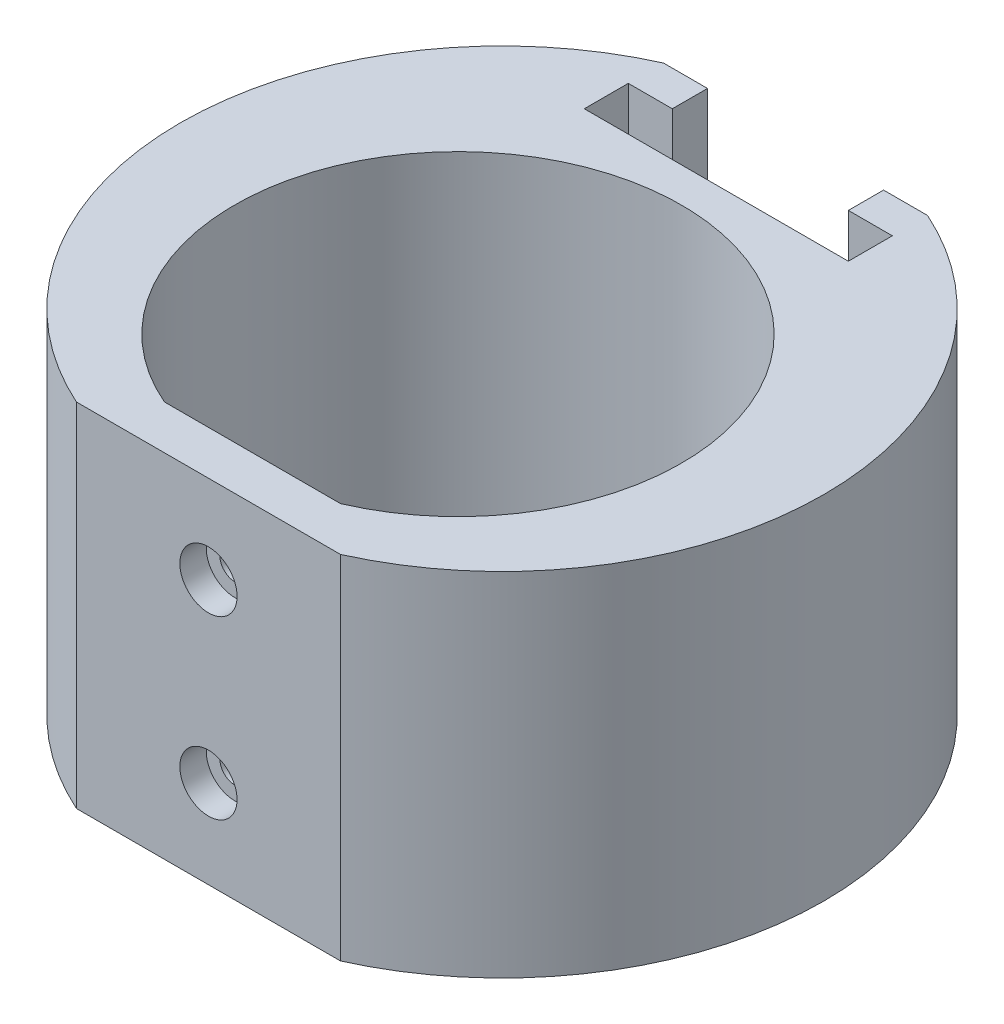
SolidWorks part; units mm, degrees
ref_plane "Front Plane" through (0, 0, 0) normal (0, 0, 1) x (1, 0, 0)
ref_plane "Top Plane" through (0, 0, 0) normal (0, 1, 0) x (1, 0, 0)
ref_plane "Right Plane" through (0, 0, 0) normal (1, 0, 0) x (0, 0, -1)
sketch "Sketch1" plane through (0, 0, 0) normal (0, 1, 0) x (1, 0, 0)
  line L0 (-10, -23.3487) -> (10, -23.3487)
  line L1 (-15, -28.3487) -> (15, -28.3487)
  line L2 (-15, 38.3487) -> (15, 38.3487)
  arc A0 (10, -23.3487) -> (-10, -23.3487) centre (0, 0) ccw
  arc A1 (15, -28.3487) -> (15, 38.3487) centre (0, 5) ccw
  arc A2 (-15, 38.3487) -> (-15, -28.3487) centre (0, 5) ccw
  dimension "D1" = 25.4
  dimension "D4" = 30
  dimension "D2" = 20
  dimension "D3" = 5
  dimension "D5" = 5
  dimension "D6" = 30
extrude "Boss-Extrude1" add sketch "Sketch1" along normal mid plane 40
ref_plane "Plane1" through (0, 0, -41.5668) normal (0, 0, -1) x (-1, 0, 0)
sketch "Sketch2" plane through (0, 0, -41.5668) normal (0, 0, -1) x (-1, 0, 0)
  line L1 (-10, -7.5) -> (10, -7.5)
  line L2 (-10, -7.5) -> (-10, 7.5)
  line L3 (-10, 7.5) -> (10, 7.5)
  line L4 (10, -7.5) -> (10, 7.5)
  line L5 (-10, -7.5) -> (10, 7.5) construction
  line L6 (-10, 7.5) -> (10, -7.5) construction
  point P0 (0, 0)
  dimension "D1" = 20
  dimension "D2" = 15
sketch "Sketch3" plane through (0, 20, 0) normal (0, 1, 0) x (1, 0, 0)
  line L0 (-10, 38.3487) -> (-10, 34.3487)
  line L2 (10, 34.3487) -> (10, 38.3487)
  line L3 (-10, 38.3487) -> (10, 38.3487)
  line L4 (15, 38.3487) -> (-15, 38.3487) construction
  line L5 (-10, 34.3487) -> (-15, 34.3487)
  line L6 (-15, 34.3487) -> (-15, 29.3487)
  line L7 (-15, 29.3487) -> (15, 29.3487)
  line L8 (15, 29.3487) -> (15, 34.3487)
  line L9 (15, 34.3487) -> (10, 34.3487)
  point P4 (0, 38.3487)
  point P5 (0, 38.3487)
  point P12 (0, 29.3487)
  dimension "D1" = 20
  dimension "D2" = 5
  dimension "D3" = 4
  dimension "D4" = 30
extrude "Cut-Extrude1" cut sketch "Sketch3" against normal up to vertex (27.5 mm away) up to point (10, -7.5, -41.5668)
fillet "Fillet1" radius 4 4 edges at (10, -7.5, -36.3487) (-10, -7.5, -36.3487) (-15, -7.5, -31.8487) (15, -7.5, -31.8487)
hole_wizard "CBORE for M3 SHCS1" positions "Sketch5" profile "Sketch6" counterbore size "M3" standard "ANSI Metric" end condition up to next
sketch "Sketch5" plane through (0, 0, 28.3487) normal (0, 0, 1) x (1, 0, 0)
  line L0 (0, 10) -> (0, -10) construction
  line L2 (-15, 20) -> (15, 20) construction
  point P0 (0, 10)
  point P2 (0, -10)
  point P12 (0, 0)
  dimension "D1" = 10
sketch "Sketch6" plane through (0, 10, 28.3487) normal (1, 0, 0) x (0, -1, 0)
  line L0 (0, 0) -> (0, 5)
  line L1 (0, 5) -> (1.7, 5)
  line L3 (1.7, 5) -> (1.7, 3)
  line L4 (1.7, 3) -> (3.25, 3)
  line L5 (3.25, 3) -> (3.25, 0)
  line L7 (3.25, 0) -> (0, 0)
  line L11 (0, -6.35) -> (0, 107.95) construction
  dimension "Thru Hole Dia." = 3.4
  dimension "Thru Hole Depth" = 5
  dimension "C'Bore Dia." = 6.5
  dimension "C'Bore Depth" = 3
hole_wizard "M3x0.5 Tapped Hole1" positions "Sketch7" profile "Sketch8" tap size "M3x0.5" standard "ANSI Metric"
sketch "Sketch7" plane through (0, 0, -38.3487) normal (0, 0, -1) x (-1, 0, 0)
  point P0 (0, 13.9088)
sketch "Sketch8" plane through (0, 13.9088, -38.3487) normal (1, 0, 0) x (0, 1, 0)
  line L0 (0, 0) -> (0, 11.7511)
  line L1 (0, 11.7511) -> (1.25, 11)
  line L2 (1.25, 11) -> (1.25, 0)
  line L3 (1.25, 0) -> (0, 0)
  line L4 (0, 11.7511) -> (-1.25, 11) construction
  line L5 (0, -6.35) -> (0, 107.95) construction
  dimension "Tap Drill Dia." = 2.5
  dimension "Tap Drill Depth" = 11
  dimension "Drill Angle" = 118
cosmetic thread "Hole Thread1" parameters "D1"=6.1, "D2"=3
